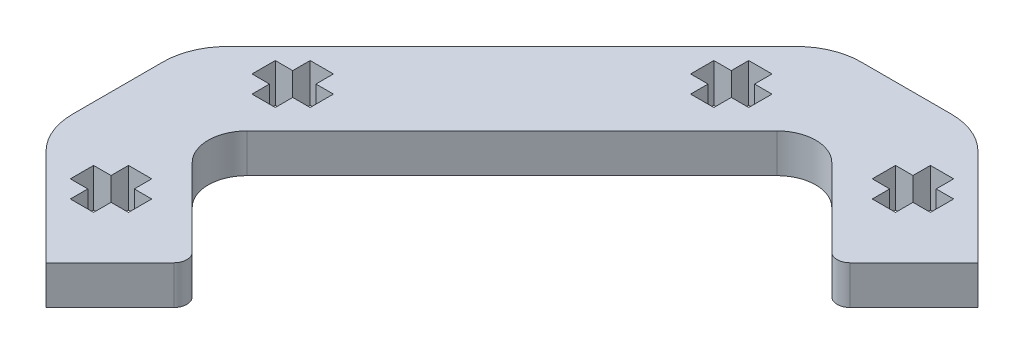
SolidWorks part; units mm, degrees
ref_plane "Front Plane" through (0, 0, 0) normal (0, 0, 1) x (1, 0, 0)
ref_plane "Top Plane" through (0, 0, 0) normal (0, 1, 0) x (1, 0, 0)
ref_plane "Right Plane" through (0, 0, 0) normal (1, 0, 0) x (0, 0, -1)
sketch "Sketch1" plane through (0, 0, 0) normal (0, 1, 0) x (1, 0, 0)
  line L0 (-6.0375, -13.9247) -> (-12.0479, -7.9143)
  line L1 (-12.0479, -3.6716) -> (8.4582, 16.8345)
  line L2 (12.7009, 16.8345) -> (18.7113, 10.8241)
  line L3 (20.1255, 10.8241) -> (25.0752, 15.7738)
  line L4 (25.0752, 15.7738) -> (17.6065, 23.2426)
  line L5 (14.0709, 24.707) -> (7.0882, 24.707)
  line L6 (3.5526, 23.2426) -> (-18.456, 1.234)
  line L7 (-19.9204, -2.3016) -> (-19.9204, -9.2843)
  line L8 (-18.456, -12.8199) -> (-10.9872, -20.2886)
  line L9 (-10.9872, -20.2886) -> (-6.0375, -15.3389)
  arc A4 (-6.0375, -15.3389) -> (-6.0375, -13.9247) centre (-6.7446, -14.6318) ccw
  arc A5 (-12.0479, -3.6716) -> (-12.0479, -7.9143) centre (-9.9265, -5.793) ccw
  arc A6 (12.7009, 16.8345) -> (8.4582, 16.8345) centre (10.5796, 14.7131) ccw
  arc A7 (18.7113, 10.8241) -> (20.1255, 10.8241) centre (19.4184, 11.5312) ccw
  arc A8 (17.6065, 23.2426) -> (14.0709, 24.707) centre (14.0709, 19.707) ccw
  arc A9 (7.0882, 24.707) -> (3.5526, 23.2426) centre (7.0882, 19.707) ccw
  arc A10 (-18.456, 1.234) -> (-19.9204, -2.3016) centre (-14.9204, -2.3016) ccw
  arc A11 (-19.9204, -9.2843) -> (-18.456, -12.8199) centre (-14.9204, -9.2843) ccw
  dimension "D2" = 51
extrude "Boss-Extrude1" add sketch "Sketch1" along normal blind 3
sketch "Sketch2" plane through (0, 3, 0) normal (0, 1, 0) x (1, 0, 0)
  line L12 (-15.6704, 2.1365) -> (-15.6704, 0.3365)
  line L13 (-15.6704, 0.3365) -> (-14.3204, 0.3365)
  line L14 (-14.3204, 0.3365) -> (-14.3204, -1.0135)
  line L15 (-14.3204, -1.0135) -> (-12.5204, -1.0135)
  line L16 (-12.5204, -1.0135) -> (-12.5204, 0.3365)
  line L17 (-12.5204, 0.3365) -> (-11.1704, 0.3365)
  line L18 (-11.1704, 0.3365) -> (-11.1704, 2.1365)
  line L19 (-11.1704, 2.1365) -> (-12.5204, 2.1365)
  line L20 (-12.5204, 2.1365) -> (-12.5204, 3.4865)
  line L21 (-12.5204, 3.4865) -> (-14.3204, 3.4865)
  line L22 (-14.3204, 3.4865) -> (-14.3204, 2.1365)
  line L23 (-14.3204, 2.1365) -> (-15.6704, 2.1365)
  line L24 (-15.6704, 2.1365) -> (-15.6704, 0.3365)
  line L25 (-15.6704, 0.3365) -> (-14.3204, 0.3365)
  line L26 (-14.3204, 0.3365) -> (-14.3204, -1.0135)
  line L27 (-14.3204, -1.0135) -> (-12.5204, -1.0135)
  line L28 (-12.5204, -1.0135) -> (-12.5204, 0.3365)
  line L29 (-12.5204, 0.3365) -> (-11.1704, 0.3365)
  line L30 (-11.1704, 0.3365) -> (-11.1704, 2.1365)
  line L31 (-11.1704, 2.1365) -> (-12.5204, 2.1365)
  line L32 (-12.5204, 2.1365) -> (-12.5204, 3.4865)
  line L33 (-12.5204, 3.4865) -> (-14.3204, 3.4865)
  line L34 (-14.3204, 3.4865) -> (-14.3204, 2.1365)
  line L35 (-14.3204, 2.1365) -> (-15.6704, 2.1365)
  line L36 (-12.5204, -10.5724) -> (-14.3204, -10.5724)
  line L37 (-14.3204, -10.5724) -> (-14.3204, -11.9224)
  line L38 (-14.3204, -11.9224) -> (-15.6704, -11.9224)
  line L39 (-15.6704, -11.9224) -> (-15.6704, -13.7224)
  line L40 (-15.6704, -13.7224) -> (-14.3204, -13.7224)
  line L41 (-14.3204, -13.7224) -> (-14.3204, -15.0724)
  line L42 (-14.3204, -15.0724) -> (-12.5204, -15.0724)
  line L43 (-12.5204, -15.0724) -> (-12.5204, -13.7224)
  line L44 (-12.5204, -13.7224) -> (-11.1704, -13.7224)
  line L45 (-11.1704, -13.7224) -> (-11.1704, -11.9224)
  line L46 (-11.1704, -11.9224) -> (-12.5204, -11.9224)
  line L47 (-12.5204, -11.9224) -> (-12.5204, -10.5724)
  line L48 (-12.5204, -10.5724) -> (-14.3204, -10.5724)
  line L49 (-14.3204, -10.5724) -> (-14.3204, -11.9224)
  line L50 (-14.3204, -11.9224) -> (-15.6704, -11.9224)
  line L51 (-15.6704, -11.9224) -> (-15.6704, -13.7224)
  line L52 (-15.6704, -13.7224) -> (-14.3204, -13.7224)
  line L53 (-14.3204, -13.7224) -> (-14.3204, -15.0724)
  line L54 (-14.3204, -15.0724) -> (-12.5204, -15.0724)
  line L55 (-12.5204, -15.0724) -> (-12.5204, -13.7224)
  line L56 (-12.5204, -13.7224) -> (-11.1704, -13.7224)
  line L57 (-11.1704, -13.7224) -> (-11.1704, -11.9224)
  line L58 (-11.1704, -11.9224) -> (-12.5204, -11.9224)
  line L59 (-12.5204, -11.9224) -> (-12.5204, -10.5724)
  line L60 (18.509, 17.307) -> (19.859, 17.307)
  line L61 (19.859, 17.307) -> (19.859, 19.107)
  line L62 (19.859, 19.107) -> (18.509, 19.107)
  line L63 (18.509, 19.107) -> (18.509, 20.457)
  line L64 (18.509, 20.457) -> (16.709, 20.457)
  line L65 (16.709, 20.457) -> (16.709, 19.107)
  line L66 (16.709, 19.107) -> (15.359, 19.107)
  line L67 (15.359, 19.107) -> (15.359, 17.307)
  line L68 (15.359, 17.307) -> (16.709, 17.307)
  line L69 (16.709, 17.307) -> (16.709, 15.957)
  line L70 (16.709, 15.957) -> (18.509, 15.957)
  line L71 (18.509, 15.957) -> (18.509, 17.307)
  line L72 (18.509, 17.307) -> (19.859, 17.307)
  line L73 (19.859, 17.307) -> (19.859, 19.107)
  line L74 (19.859, 19.107) -> (18.509, 19.107)
  line L75 (18.509, 19.107) -> (18.509, 20.457)
  line L76 (18.509, 20.457) -> (16.709, 20.457)
  line L77 (16.709, 20.457) -> (16.709, 19.107)
  line L78 (16.709, 19.107) -> (15.359, 19.107)
  line L79 (15.359, 19.107) -> (15.359, 17.307)
  line L80 (15.359, 17.307) -> (16.709, 17.307)
  line L81 (16.709, 17.307) -> (16.709, 15.957)
  line L82 (16.709, 15.957) -> (18.509, 15.957)
  line L83 (18.509, 15.957) -> (18.509, 17.307)
  line L84 (36.8296, -13.7224) -> (36.8296, -11.9224)
  line L85 (36.8296, -11.9224) -> (35.4796, -11.9224)
  line L86 (35.4796, -11.9224) -> (35.4796, -10.5724)
  line L87 (35.4796, -10.5724) -> (33.6796, -10.5724)
  line L88 (33.6796, -10.5724) -> (33.6796, -11.9224)
  line L89 (33.6796, -11.9224) -> (32.3296, -11.9224)
  line L90 (32.3296, -11.9224) -> (32.3296, -13.7224)
  line L91 (32.3296, -13.7224) -> (33.6796, -13.7224)
  line L92 (33.6796, -13.7224) -> (33.6796, -15.0724)
  line L93 (33.6796, -15.0724) -> (35.4796, -15.0724)
  line L94 (35.4796, -15.0724) -> (35.4796, -13.7224)
  line L95 (35.4796, -13.7224) -> (36.8296, -13.7224)
  line L96 (36.8296, -13.7224) -> (36.8296, -11.9224)
  line L97 (36.8296, -11.9224) -> (35.4796, -11.9224)
  line L98 (35.4796, -11.9224) -> (35.4796, -10.5724)
  line L99 (35.4796, -10.5724) -> (33.6796, -10.5724)
  line L100 (33.6796, -10.5724) -> (33.6796, -11.9224)
  line L101 (33.6796, -11.9224) -> (32.3296, -11.9224)
  line L102 (32.3296, -11.9224) -> (32.3296, -13.7224)
  line L103 (32.3296, -13.7224) -> (33.6796, -13.7224)
  line L104 (33.6796, -13.7224) -> (33.6796, -15.0724)
  line L105 (33.6796, -15.0724) -> (35.4796, -15.0724)
  line L106 (35.4796, -15.0724) -> (35.4796, -13.7224)
  line L107 (35.4796, -13.7224) -> (36.8296, -13.7224)
  line L108 (5.8001, 19.107) -> (4.4501, 19.107)
  line L109 (4.4501, 19.107) -> (4.4501, 20.457)
  line L110 (4.4501, 20.457) -> (2.6501, 20.457)
  line L111 (2.6501, 20.457) -> (2.6501, 19.107)
  line L112 (2.6501, 19.107) -> (1.3001, 19.107)
  line L113 (1.3001, 19.107) -> (1.3001, 17.307)
  line L114 (1.3001, 17.307) -> (2.6501, 17.307)
  line L115 (2.6501, 17.307) -> (2.6501, 15.957)
  line L116 (2.6501, 15.957) -> (4.4501, 15.957)
  line L117 (4.4501, 15.957) -> (4.4501, 17.307)
  line L118 (4.4501, 17.307) -> (5.8001, 17.307)
  line L119 (5.8001, 17.307) -> (5.8001, 19.107)
  line L120 (5.8001, 19.107) -> (4.4501, 19.107)
  line L121 (4.4501, 19.107) -> (4.4501, 20.457)
  line L122 (4.4501, 20.457) -> (2.6501, 20.457)
  line L123 (2.6501, 20.457) -> (2.6501, 19.107)
  line L124 (2.6501, 19.107) -> (1.3001, 19.107)
  line L125 (1.3001, 19.107) -> (1.3001, 17.307)
  line L126 (1.3001, 17.307) -> (2.6501, 17.307)
  line L127 (2.6501, 17.307) -> (2.6501, 15.957)
  line L128 (2.6501, 15.957) -> (4.4501, 15.957)
  line L129 (4.4501, 15.957) -> (4.4501, 17.307)
  line L130 (4.4501, 17.307) -> (5.8001, 17.307)
  line L131 (5.8001, 17.307) -> (5.8001, 19.107)
  line L132 (36.8296, 2.1365) -> (35.4796, 2.1365)
  line L133 (36.8296, 0.3365) -> (36.8296, 2.1365)
  line L134 (35.4796, 0.3365) -> (36.8296, 0.3365)
  line L135 (35.4796, -1.0135) -> (35.4796, 0.3365)
  line L136 (33.6796, -1.0135) -> (35.4796, -1.0135)
  line L137 (33.6796, 0.3365) -> (33.6796, -1.0135)
  line L138 (32.3296, 0.3365) -> (33.6796, 0.3365)
  line L139 (32.3296, 2.1365) -> (32.3296, 0.3365)
  line L140 (33.6796, 2.1365) -> (32.3296, 2.1365)
  line L141 (33.6796, 3.4865) -> (33.6796, 2.1365)
  line L142 (35.4796, 3.4865) -> (33.6796, 3.4865)
  line L143 (35.4796, 2.1365) -> (35.4796, 3.4865)
  line L144 (36.8296, 2.1365) -> (35.4796, 2.1365)
  line L145 (36.8296, 0.3365) -> (36.8296, 2.1365)
  line L146 (35.4796, 0.3365) -> (36.8296, 0.3365)
  line L147 (35.4796, -1.0135) -> (35.4796, 0.3365)
  line L148 (33.6796, -1.0135) -> (35.4796, -1.0135)
  line L149 (33.6796, 0.3365) -> (33.6796, -1.0135)
  line L150 (32.3296, 0.3365) -> (33.6796, 0.3365)
  line L151 (32.3296, 2.1365) -> (32.3296, 0.3365)
  line L152 (33.6796, 2.1365) -> (32.3296, 2.1365)
  line L153 (33.6796, 3.4865) -> (33.6796, 2.1365)
  line L154 (35.4796, 3.4865) -> (33.6796, 3.4865)
  line L155 (35.4796, 2.1365) -> (35.4796, 3.4865)
  line L156 (4.4501, -32.043) -> (4.4501, -30.693)
  line L157 (4.4501, -30.693) -> (5.8001, -30.693)
  line L158 (5.8001, -30.693) -> (5.8001, -28.893)
  line L159 (5.8001, -28.893) -> (4.4501, -28.893)
  line L160 (4.4501, -28.893) -> (4.4501, -27.543)
  line L161 (4.4501, -27.543) -> (2.6501, -27.543)
  line L162 (2.6501, -27.543) -> (2.6501, -28.893)
  line L163 (2.6501, -28.893) -> (1.3001, -28.893)
  line L164 (1.3001, -28.893) -> (1.3001, -30.693)
  line L165 (1.3001, -30.693) -> (2.6501, -30.693)
  line L166 (2.6501, -30.693) -> (2.6501, -32.043)
  line L167 (2.6501, -32.043) -> (4.4501, -32.043)
  line L168 (4.4501, -32.043) -> (4.4501, -30.693)
  line L169 (4.4501, -30.693) -> (5.8001, -30.693)
  line L170 (5.8001, -30.693) -> (5.8001, -28.893)
  line L171 (5.8001, -28.893) -> (4.4501, -28.893)
  line L172 (4.4501, -28.893) -> (4.4501, -27.543)
  line L173 (4.4501, -27.543) -> (2.6501, -27.543)
  line L174 (2.6501, -27.543) -> (2.6501, -28.893)
  line L175 (2.6501, -28.893) -> (1.3001, -28.893)
  line L176 (1.3001, -28.893) -> (1.3001, -30.693)
  line L177 (1.3001, -30.693) -> (2.6501, -30.693)
  line L178 (2.6501, -30.693) -> (2.6501, -32.043)
  line L179 (2.6501, -32.043) -> (4.4501, -32.043)
  line L180 (18.509, -32.043) -> (18.509, -30.693)
  line L181 (18.509, -30.693) -> (19.859, -30.693)
  line L182 (19.859, -30.693) -> (19.859, -28.893)
  line L183 (19.859, -28.893) -> (18.509, -28.893)
  line L184 (18.509, -28.893) -> (18.509, -27.543)
  line L185 (18.509, -27.543) -> (16.709, -27.543)
  line L186 (16.709, -27.543) -> (16.709, -28.893)
  line L187 (16.709, -28.893) -> (15.359, -28.893)
  line L188 (15.359, -28.893) -> (15.359, -30.693)
  line L189 (15.359, -30.693) -> (16.709, -30.693)
  line L190 (16.709, -30.693) -> (16.709, -32.043)
  line L191 (16.709, -32.043) -> (18.509, -32.043)
  line L192 (18.509, -32.043) -> (18.509, -30.693)
  line L193 (18.509, -30.693) -> (19.859, -30.693)
  line L194 (19.859, -30.693) -> (19.859, -28.893)
  line L195 (19.859, -28.893) -> (18.509, -28.893)
  line L196 (18.509, -28.893) -> (18.509, -27.543)
  line L197 (18.509, -27.543) -> (16.709, -27.543)
  line L198 (16.709, -27.543) -> (16.709, -28.893)
  line L199 (16.709, -28.893) -> (15.359, -28.893)
  line L200 (15.359, -28.893) -> (15.359, -30.693)
  line L201 (15.359, -30.693) -> (16.709, -30.693)
  line L202 (16.709, -30.693) -> (16.709, -32.043)
  line L203 (16.709, -32.043) -> (18.509, -32.043)
  dimension "D1" = 0
  dimension "D2" = 0
  dimension "D3" = 0
  dimension "D4" = 0
  dimension "D5" = 0
  dimension "D6" = 0
  dimension "D7" = 0
  dimension "D8" = 0
extrude "Cut-Extrude1" cut sketch "Sketch2" against normal through all
sketch "Sketch3" plane through (0, 3, 0) normal (0, 1, 0) x (1, 0, 0)
  line L12 (4.4501, 19.107) -> (4.4501, 20.457)
  line L13 (5.8001, 19.107) -> (4.4501, 19.107)
  line L14 (5.8001, 17.307) -> (5.8001, 19.107)
  line L15 (4.4501, 17.307) -> (5.8001, 17.307)
  line L16 (4.4501, 15.957) -> (4.4501, 17.307)
  line L17 (2.6501, 15.957) -> (4.4501, 15.957)
  line L18 (2.6501, 17.307) -> (2.6501, 15.957)
  line L19 (1.3001, 17.307) -> (2.6501, 17.307)
  line L20 (1.3001, 19.107) -> (1.3001, 17.307)
  line L21 (2.6501, 19.107) -> (1.3001, 19.107)
  line L22 (2.6501, 20.457) -> (2.6501, 19.107)
  line L23 (4.4501, 20.457) -> (2.6501, 20.457)
  line L24 (4.4501, 19.107) -> (4.4501, 20.457)
  line L25 (5.8001, 19.107) -> (4.4501, 19.107)
  line L26 (5.8001, 17.307) -> (5.8001, 19.107)
  line L27 (4.4501, 17.307) -> (5.8001, 17.307)
  line L28 (4.4501, 15.957) -> (4.4501, 17.307)
  line L29 (2.6501, 15.957) -> (4.4501, 15.957)
  line L30 (2.6501, 17.307) -> (2.6501, 15.957)
  line L31 (1.3001, 17.307) -> (2.6501, 17.307)
  line L32 (1.3001, 19.107) -> (1.3001, 17.307)
  line L33 (2.6501, 19.107) -> (1.3001, 19.107)
  line L34 (2.6501, 20.457) -> (2.6501, 19.107)
  line L35 (4.4501, 20.457) -> (2.6501, 20.457)
  line L36 (-14.3204, 2.1365) -> (-15.6704, 2.1365)
  line L37 (-14.3204, 3.4865) -> (-14.3204, 2.1365)
  line L38 (-12.5204, 3.4865) -> (-14.3204, 3.4865)
  line L39 (-12.5204, 2.1365) -> (-12.5204, 3.4865)
  line L40 (-11.1704, 2.1365) -> (-12.5204, 2.1365)
  line L41 (-11.1704, 0.3365) -> (-11.1704, 2.1365)
  line L42 (-12.5204, 0.3365) -> (-11.1704, 0.3365)
  line L43 (-12.5204, -1.0135) -> (-12.5204, 0.3365)
  line L44 (-14.3204, -1.0135) -> (-12.5204, -1.0135)
  line L45 (-14.3204, 0.3365) -> (-14.3204, -1.0135)
  line L46 (-15.6704, 0.3365) -> (-14.3204, 0.3365)
  line L47 (-15.6704, 2.1365) -> (-15.6704, 0.3365)
  line L48 (-14.3204, 2.1365) -> (-15.6704, 2.1365)
  line L49 (-14.3204, 3.4865) -> (-14.3204, 2.1365)
  line L50 (-12.5204, 3.4865) -> (-14.3204, 3.4865)
  line L51 (-12.5204, 2.1365) -> (-12.5204, 3.4865)
  line L52 (-11.1704, 2.1365) -> (-12.5204, 2.1365)
  line L53 (-11.1704, 0.3365) -> (-11.1704, 2.1365)
  line L54 (-12.5204, 0.3365) -> (-11.1704, 0.3365)
  line L55 (-12.5204, -1.0135) -> (-12.5204, 0.3365)
  line L56 (-14.3204, -1.0135) -> (-12.5204, -1.0135)
  line L57 (-14.3204, 0.3365) -> (-14.3204, -1.0135)
  line L58 (-15.6704, 0.3365) -> (-14.3204, 0.3365)
  line L59 (-15.6704, 2.1365) -> (-15.6704, 0.3365)
  line L60 (-14.3204, -10.5724) -> (-14.3204, -11.9224)
  line L61 (-12.5204, -10.5724) -> (-14.3204, -10.5724)
  line L62 (-12.5204, -11.9224) -> (-12.5204, -10.5724)
  line L63 (-11.1704, -11.9224) -> (-12.5204, -11.9224)
  line L64 (-11.1704, -13.7224) -> (-11.1704, -11.9224)
  line L65 (-12.5204, -13.7224) -> (-11.1704, -13.7224)
  line L66 (-12.5204, -15.0724) -> (-12.5204, -13.7224)
  line L67 (-14.3204, -15.0724) -> (-12.5204, -15.0724)
  line L68 (-14.3204, -13.7224) -> (-14.3204, -15.0724)
  line L69 (-15.6704, -13.7224) -> (-14.3204, -13.7224)
  line L70 (-15.6704, -11.9224) -> (-15.6704, -13.7224)
  line L71 (-14.3204, -11.9224) -> (-15.6704, -11.9224)
  line L72 (-14.3204, -10.5724) -> (-14.3204, -11.9224)
  line L73 (-12.5204, -10.5724) -> (-14.3204, -10.5724)
  line L74 (-12.5204, -11.9224) -> (-12.5204, -10.5724)
  line L75 (-11.1704, -11.9224) -> (-12.5204, -11.9224)
  line L76 (-11.1704, -13.7224) -> (-11.1704, -11.9224)
  line L77 (-12.5204, -13.7224) -> (-11.1704, -13.7224)
  line L78 (-12.5204, -15.0724) -> (-12.5204, -13.7224)
  line L79 (-14.3204, -15.0724) -> (-12.5204, -15.0724)
  line L80 (-14.3204, -13.7224) -> (-14.3204, -15.0724)
  line L81 (-15.6704, -13.7224) -> (-14.3204, -13.7224)
  line L82 (-15.6704, -11.9224) -> (-15.6704, -13.7224)
  line L83 (-14.3204, -11.9224) -> (-15.6704, -11.9224)
  line L84 (18.509, 15.957) -> (18.509, 17.307)
  line L85 (16.709, 15.957) -> (18.509, 15.957)
  line L86 (16.709, 17.307) -> (16.709, 15.957)
  line L87 (15.359, 17.307) -> (16.709, 17.307)
  line L88 (15.359, 19.107) -> (15.359, 17.307)
  line L89 (16.709, 19.107) -> (15.359, 19.107)
  line L90 (16.709, 20.457) -> (16.709, 19.107)
  line L91 (18.509, 20.457) -> (16.709, 20.457)
  line L92 (18.509, 19.107) -> (18.509, 20.457)
  line L93 (19.859, 19.107) -> (18.509, 19.107)
  line L94 (19.859, 17.307) -> (19.859, 19.107)
  line L95 (18.509, 17.307) -> (19.859, 17.307)
  line L96 (18.509, 15.957) -> (18.509, 17.307)
  line L97 (16.709, 15.957) -> (18.509, 15.957)
  line L98 (16.709, 17.307) -> (16.709, 15.957)
  line L99 (15.359, 17.307) -> (16.709, 17.307)
  line L100 (15.359, 19.107) -> (15.359, 17.307)
  line L101 (16.709, 19.107) -> (15.359, 19.107)
  line L102 (16.709, 20.457) -> (16.709, 19.107)
  line L103 (18.509, 20.457) -> (16.709, 20.457)
  line L104 (18.509, 19.107) -> (18.509, 20.457)
  line L105 (19.859, 19.107) -> (18.509, 19.107)
  line L106 (19.859, 17.307) -> (19.859, 19.107)
  line L107 (18.509, 17.307) -> (19.859, 17.307)
  line L116 (-6.0375, -13.9247) -> (-12.0479, -7.9143)
  line L117 (-12.0479, -3.6716) -> (8.4582, 16.8345)
  line L118 (12.7009, 16.8345) -> (18.7113, 10.8241)
  line L119 (20.1255, 10.8241) -> (25.0752, 15.7738)
  line L120 (25.0752, 15.7738) -> (17.6065, 23.2426)
  line L121 (14.0709, 24.707) -> (7.0882, 24.707)
  line L122 (3.5526, 23.2426) -> (-18.456, 1.234)
  line L123 (-19.9204, -2.3016) -> (-19.9204, -9.2843)
  line L124 (-18.456, -12.8199) -> (-10.9872, -20.2886)
  line L125 (-10.9872, -20.2886) -> (-6.0375, -15.3389)
  line L126 (-6.0375, -13.9247) -> (-12.0479, -7.9143)
  line L127 (-12.0479, -3.6716) -> (8.4582, 16.8345)
  line L128 (12.7009, 16.8345) -> (18.7113, 10.8241)
  line L129 (20.1255, 10.8241) -> (25.0752, 15.7738)
  line L130 (25.0752, 15.7738) -> (17.6065, 23.2426)
  line L131 (14.0709, 24.707) -> (7.0882, 24.707)
  line L132 (3.5526, 23.2426) -> (-18.456, 1.234)
  line L133 (-19.9204, -2.3016) -> (-19.9204, -9.2843)
  line L134 (-18.456, -12.8199) -> (-10.9872, -20.2886)
  line L135 (-10.9872, -20.2886) -> (-6.0375, -15.3389)
  arc A16 (-6.0375, -15.3389) -> (-6.0375, -13.9247) centre (-6.7446, -14.6318) ccw
  arc A17 (-12.0479, -3.6716) -> (-12.0479, -7.9143) centre (-9.9265, -5.793) ccw
  arc A18 (12.7009, 16.8345) -> (8.4582, 16.8345) centre (10.5796, 14.7131) ccw
  arc A19 (18.7113, 10.8241) -> (20.1255, 10.8241) centre (19.4184, 11.5312) ccw
  arc A20 (17.6065, 23.2426) -> (14.0709, 24.707) centre (14.0709, 19.707) ccw
  arc A21 (7.0882, 24.707) -> (3.5526, 23.2426) centre (7.0882, 19.707) ccw
  arc A22 (-18.456, 1.234) -> (-19.9204, -2.3016) centre (-14.9204, -2.3016) ccw
  arc A23 (-19.9204, -9.2843) -> (-18.456, -12.8199) centre (-14.9204, -9.2843) ccw
  arc A24 (-6.0375, -15.3389) -> (-6.0375, -13.9247) centre (-6.7446, -14.6318) ccw
  arc A25 (-12.0479, -3.6716) -> (-12.0479, -7.9143) centre (-9.9265, -5.793) ccw
  arc A26 (12.7009, 16.8345) -> (8.4582, 16.8345) centre (10.5796, 14.7131) ccw
  arc A27 (18.7113, 10.8241) -> (20.1255, 10.8241) centre (19.4184, 11.5312) ccw
  arc A28 (17.6065, 23.2426) -> (14.0709, 24.707) centre (14.0709, 19.707) ccw
  arc A29 (7.0882, 24.707) -> (3.5526, 23.2426) centre (7.0882, 19.707) ccw
  arc A30 (-18.456, 1.234) -> (-19.9204, -2.3016) centre (-14.9204, -2.3016) ccw
  arc A31 (-19.9204, -9.2843) -> (-18.456, -12.8199) centre (-14.9204, -9.2843) ccw
  dimension "D1" = 0
  dimension "D2" = 0
  dimension "D3" = 0
  dimension "D4" = 0
  dimension "D5" = 0
